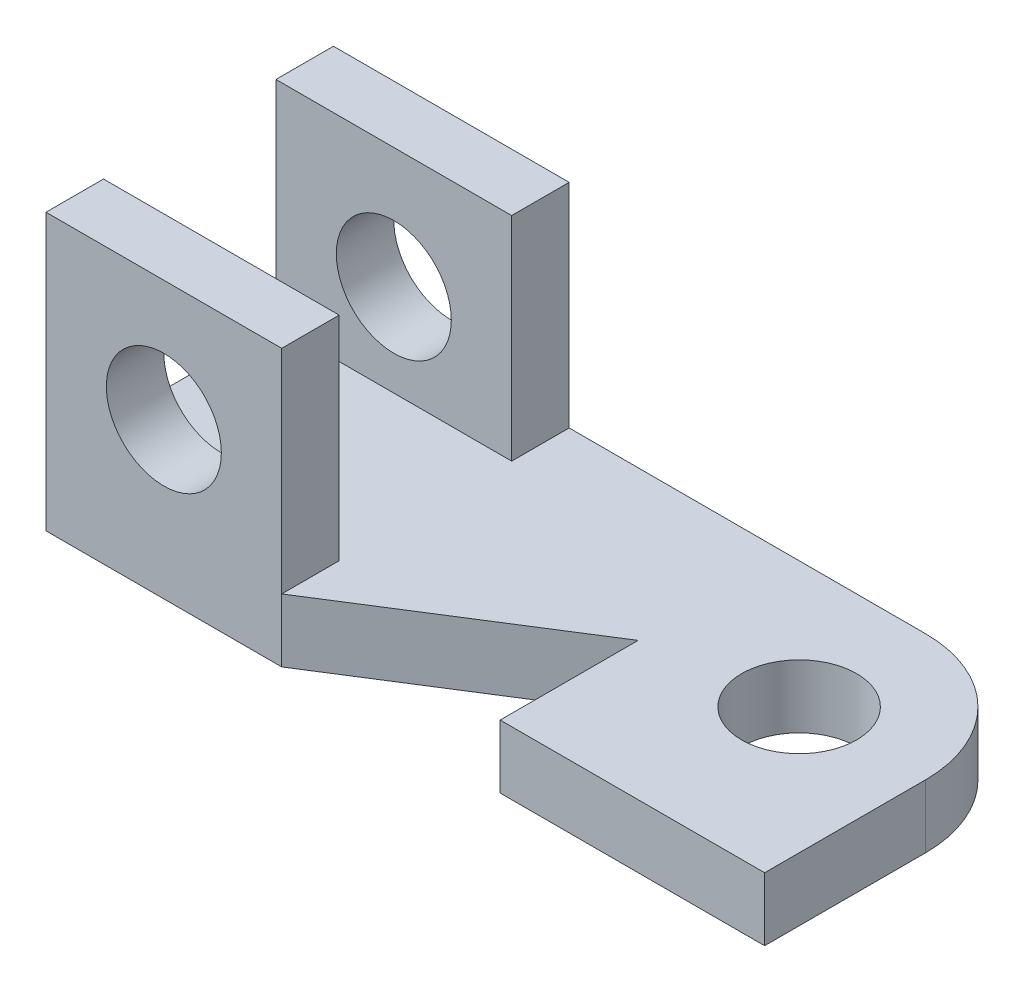
SolidWorks part; units mm, degrees
ref_plane "Front Plane" through (0, 0, 0) normal (0, 0, 1) x (1, 0, 0)
ref_plane "Top Plane" through (0, 0, 0) normal (0, 1, 0) x (1, 0, 0)
ref_plane "Right Plane" through (0, 0, 0) normal (1, 0, 0) x (0, 0, -1)
sketch "Sketch1" plane through (0, 0, 0) normal (0, 1, 0) x (1, 0, 0)
  line L0 (-460, 0) -> (-460, 240)
  line L1 (0, 0) -> (-460, 0)
  line L2 (0, 0) -> (0, 280)
  line L3 (-220, 500) -> (-1250, 500)
  line L4 (-1250, 0) -> (-1250, 500)
  line L5 (0, 0) -> (-1250, 500) construction
  line L6 (-95.8845, 461.6462) -> (-1250, 0) construction
  line L7 (-460, 240) -> (-840, 0)
  line L8 (-840, 0) -> (-1250, 0)
  circle A0 centre (-220, 280) radius 100
  arc A1 (-220, 500) -> (0, 280) centre (-220, 280) cw
  point P4 (-625, 250)
  dimension "D3" = 200
  dimension "D8" = 220
  dimension "D1" = 500
  dimension "D2" = 1250
  dimension "D4" = 220
  dimension "D5" = 240
  dimension "D6" = 380
  dimension "D7" = 460
  dimension "D9" = 220
extrude "Boss-Extrude1" add sketch "Sketch1" along normal blind 110 contours L2 A1 L3 L4 L8 L7 L0 L1 | A0
sketch "Sketch2" plane through (0, 110, 0) normal (0, 1, 0) x (1, 0, 0)
  line L0 (-1250, 100) -> (-840, 100)
  line L1 (-1250, 0) -> (-1250, 500) construction
  line L2 (-840, 100) -> (-840, 0)
  line L3 (-1250, 400) -> (-840, 400)
  line L4 (-840, 400) -> (-840, 500)
  line L5 (-220, 500) -> (-1250, 500) construction
  line M6 (-220, 500) -> (-1250, 500)
  line M7 (-1250, 500) -> (-1250, 0)
  line M8 (-1250, 0) -> (-840, 0)
  dimension "D1" = 100
  dimension "D2" = 100
  dimension "D3" = 410
extrude "Boss-Extrude2" add sketch "Sketch2" along normal blind 370 contours L3 L4 M6 M7 | L2 L0 M7 M8
sketch "Sketch3" plane through (0, 0, 0) normal (0, 0, 1) x (1, 0, 0)
  line L0 (-1250, 480) -> (-840, 480) construction
  line L1 (-1250, 480) -> (-1250, 0) construction
  circle A0 centre (-1045, 270) radius 100
  point P4 (0, 0)
  point P6 (-1100.422, 274.8024)
  dimension "D1" = 200
  dimension "D2" = 210
  dimension "D3" = 205
extrude "Cut-Extrude1" cut sketch "Sketch3" against normal through all contours A0
equation "\"11cmcm\"=1"
